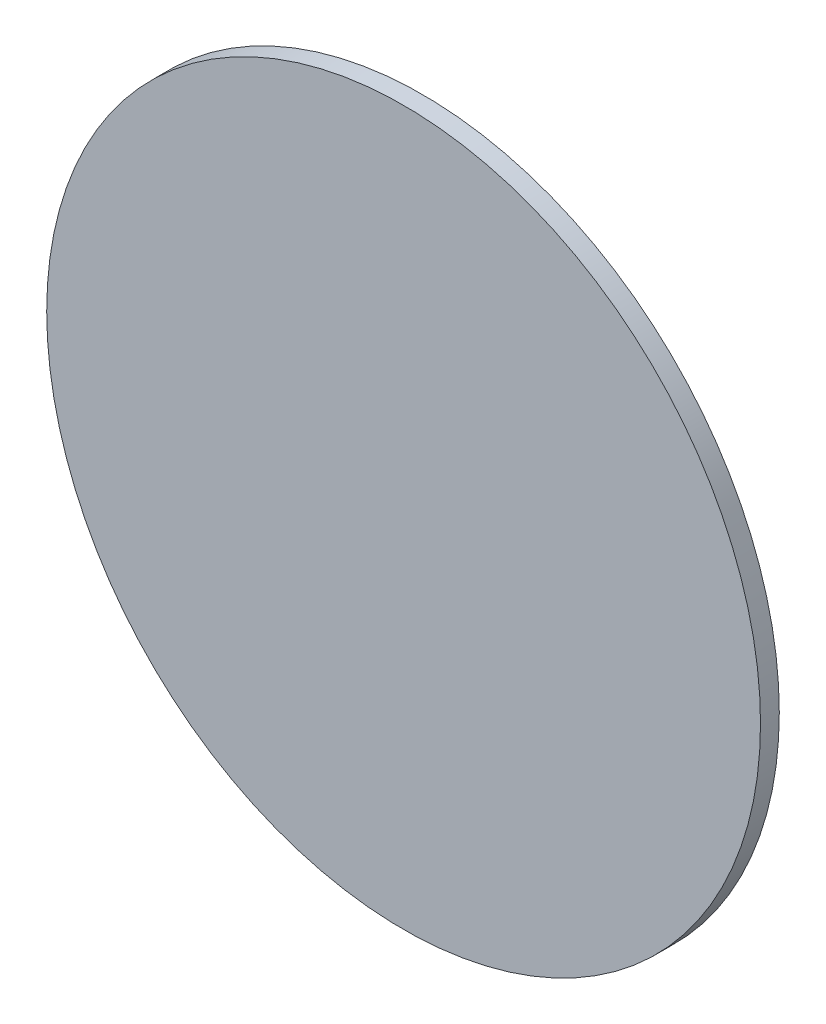
SolidWorks part; units mm, degrees
material "3.0205 (EN-AW 1200)"
ref_plane "Alzado" through (0, 0, 0) normal (0, 0, 1) x (1, 0, 0)
ref_plane "Planta" through (0, 0, 0) normal (0, 1, 0) x (1, 0, 0)
ref_plane "Vista lateral" through (0, 0, 0) normal (1, 0, 0) x (0, 0, -1)
sketch "Croquis1" plane through (0, 0, 0) normal (0, 0, 1) x (1, 0, 0)
  circle A0 centre (0, 0) radius 7.6
  dimension "D1" = 15.2
extrude "Saliente-Extruir1" add sketch "Croquis1" along normal blind 0.4
